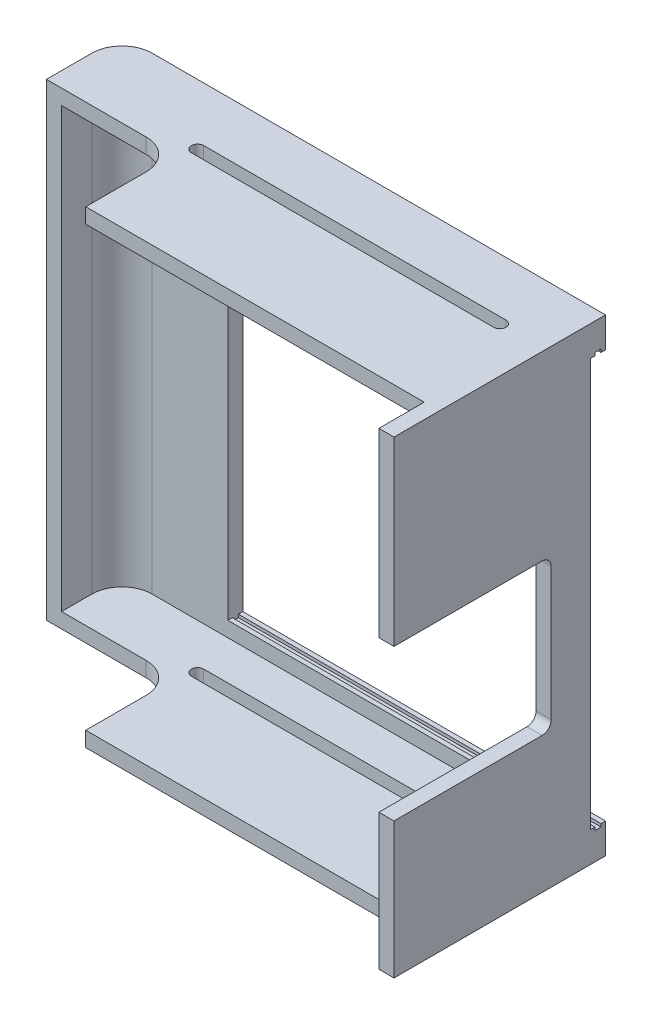
SolidWorks part; units mm, degrees
ref_plane "Front Plane" through (0, 0, 0) normal (0, 0, 1) x (1, 0, 0)
ref_plane "Top Plane" through (0, 0, 0) normal (0, 1, 0) x (1, 0, 0)
ref_plane "Right Plane" through (0, 0, 0) normal (1, 0, 0) x (0, 0, -1)
sketch "Sketch1" plane through (0, 0, 0) normal (0, 1, 0) x (1, 0, 0)
  line L1 (-86.5373, 36.1567) -> (63.4627, 36.1567)
  line L2 (-86.5373, 36.1567) -> (-86.5373, -18.8433)
  line L3 (-86.5373, -18.8433) -> (63.4627, -18.8433)
  line L4 (63.4627, 36.1567) -> (63.4627, -18.8433)
  line L5 (-86.5373, 11.1567) -> (-48.5373, 11.1567)
  line L6 (-86.5373, 11.1567) -> (-86.5373, -18.8433)
  line L7 (-86.5373, -18.8433) -> (-48.5373, -18.8433)
  line L8 (-48.5373, 11.1567) -> (-48.5373, -18.8433)
  dimension "D1" = 55
  dimension "D2" = 150
  dimension "D3" = 25
  dimension "D4" = 38
extrude "Boss-Extrude1" add sketch "Sketch1" along normal blind 5 contours L5 L8 L3 L4 L1 L2
sketch "Sketch2" plane through (0, 5, 0) normal (0, 1, 0) x (1, 0, 0)
  line L0 (63.4627, 36.1567) -> (63.4627, -18.8433) construction
  line L1 (-86.5373, 36.1567) -> (63.4627, 36.1567)
  line L2 (-86.5373, 36.1567) -> (-86.5373, 31.1567)
  line L3 (-86.5373, 31.1567) -> (63.4627, 31.1567)
  line L4 (63.4627, 36.1567) -> (63.4627, 31.1567)
  dimension "D1" = 5
extrude "Boss-Extrude2" add sketch "Sketch2" along normal blind 145
sketch "Sketch4" plane through (0, 0, -31.1567) normal (0, 0, 1) x (1, 0, 0)
  line L0 (63.4627, 77.5) -> (-86.5373, 77.5) construction
  line L1 (63.4627, 150) -> (63.4627, 5) construction
  line L2 (-86.5373, 150) -> (-86.5373, 5) construction
ref_plane "Plane1" through (0, 77.5, 0) normal (0, 1, 0) x (-1, 0, 0)
mirror "Mirror1" about plane through (0, 77.5, 0) normal (0, 1, 0) of "Boss-Extrude1"
ref_plane "Plane2" through (63.4627, 150, -31.1567) normal (0, -1, 0) x (-1, 0, 0)
sketch "Sketch6" plane through (63.4627, 0, 0) normal (1, 0, 0) x (0, 0, -1)
  line L1 (36.1567, 155) -> (-33.8433, 155)
  line L2 (36.1567, 155) -> (36.1567, 0)
  line L3 (36.1567, 0) -> (-33.8433, 0)
  line L4 (-33.8433, 155) -> (-33.8433, 0)
  line L5 (36.1567, 0) -> (-18.8433, 0) construction
  dimension "D1" = 70
extrude "Boss-Extrude3" add sketch "Sketch6" along normal blind 5
sketch "Sketch7" plane through (68.4627, 0, 0) normal (1, 0, 0) x (0, 0, -1)
  line L0 (-33.8433, 155) -> (-33.8433, 0) construction
  line L1 (-33.8433, 95) -> (18.1567, 95)
  line L2 (-33.8433, 95) -> (-33.8433, 45)
  line L3 (-33.8433, 45) -> (18.1567, 45)
  line L4 (18.1567, 95) -> (18.1567, 45)
  line L6 (36.1567, 0) -> (36.1567, 155) construction
  line L7 (-33.8433, 0) -> (36.1567, 0) construction
  dimension "D1" = 50
  dimension "D2" = 45
  dimension "D3" = 18
extrude "Cut-Extrude1" cut sketch "Sketch7" against normal blind 5
sketch "Sketch8" plane through (-86.5373, 0, 0) normal (-1, 0, 0) x (0, 0, 1)
  line L1 (-36.1567, 0) -> (-11.1567, 0)
  line L2 (-36.1567, 0) -> (-36.1567, 155)
  line L3 (-36.1567, 155) -> (-11.1567, 155)
  line L4 (-11.1567, 0) -> (-11.1567, 155)
extrude "Boss-Extrude4" add sketch "Sketch8" along normal blind 5
fillet "Fillet1" radius 10 3 edges at (-48.5373, 2.5, -11.1567) (-48.5373, 152.5, -11.1567) (-91.5373, 77.5, -36.1567)
fillet "Fillet2" radius 10 1 edges at (-86.5373, 77.5, -31.1567)
sketch "Sketch9" plane through (68.4627, 0, 0) normal (1, 0, 0) x (0, 0, -1)
  line L0 (36.1567, 0) -> (36.1567, 155) construction
  line L1 (36.1567, 145) -> (31.1567, 145)
  line L2 (36.1567, 145) -> (36.1567, 10)
  line L3 (36.1567, 10) -> (31.1567, 10)
  line L4 (31.1567, 145) -> (31.1567, 10)
  line L5 (36.1567, 155) -> (-33.8433, 155) construction
  line L6 (-33.8433, 0) -> (36.1567, 0) construction
  line L7 (81.95, 77.5) -> (-81.95, 77.5) construction
  line L8 (34.6567, 145) -> (32.6567, 145)
  line L9 (34.6567, 145) -> (34.6567, 146)
  line L10 (34.6567, 146) -> (32.6567, 146)
  line L11 (32.6567, 145) -> (32.6567, 146)
  line L12 (34.6567, 9) -> (32.6567, 9)
  line L13 (32.6567, 10) -> (32.6567, 9)
  line L14 (34.6567, 10) -> (32.6567, 10)
  line L15 (34.6567, 10) -> (34.6567, 9)
  line M15 (36.1567, 0) -> (36.1567, 155)
  dimension "D1" = 5
  dimension "D2" = 10
  dimension "D3" = 10
  dimension "D4" = 2
  dimension "D5" = 1.5
  dimension "D6" = 1
extrude "Cut-Extrude2" cut sketch "Sketch9" against normal blind 120 contours L1 L4 L3 M15 | L15 L3 L13 L12 | L11 L1 L9 L10
fillet "Fillet5" radius 3 2 edges at (65.9627, 45, -18.1567) (65.9627, 95, -18.1567)
sketch "Sketch11" plane through (0, 0, 0) normal (0, -1, 0) x (1, 0, 0)
  line L0 (53.4627, -16.1567) -> (-46.5373, -16.1567) construction
  line L1 (53.4627, -18.2067) -> (-46.5373, -18.2067)
  line L2 (53.4627, -14.1067) -> (-46.5373, -14.1067)
  line L3 (68.4627, 33.8433) -> (68.4627, -36.1567) construction
  line L4 (-81.5373, -36.1567) -> (68.4627, -36.1567) construction
  arc A0 (53.4627, -18.2067) -> (53.4627, -14.1067) centre (53.4627, -16.1567) ccw
  arc A1 (-46.5373, -14.1067) -> (-46.5373, -18.2067) centre (-46.5373, -16.1567) ccw
  point P2 (3.4627, -16.1567)
  dimension "D1" = 4.1
  dimension "D2" = 100
  dimension "D3" = 65
  dimension "D4" = 20
extrude "Cut-Extrude4" cut sketch "Sketch11" against normal up to surface (155 mm away)
